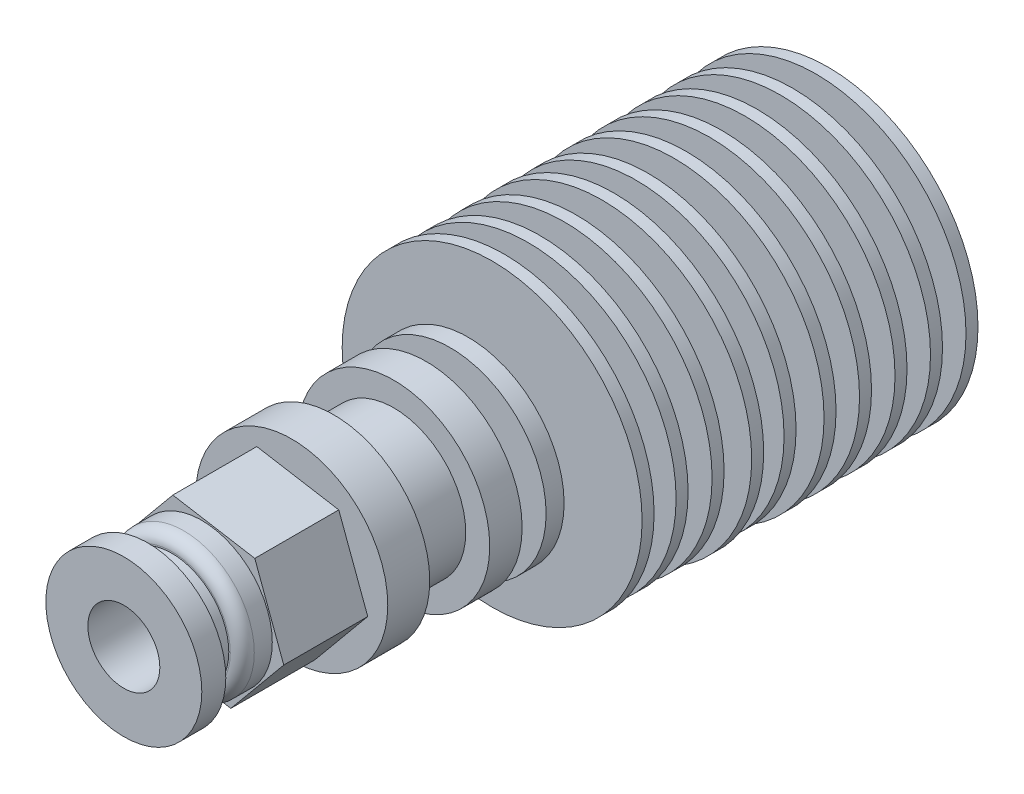
SolidWorks part; units mm, degrees
ref_plane "Front Plane" through (0, 0, 0) normal (0, 0, 1) x (1, 0, 0)
ref_plane "Top Plane" through (0, 0, 0) normal (0, 1, 0) x (1, 0, 0)
ref_plane "Right Plane" through (0, 0, 0) normal (1, 0, 0) x (0, 0, -1)
sketch "Sketch1" plane through (0, 0, 0) normal (0, 0, 1) x (1, 0, 0)
  circle A0 centre (0, 0) radius 12.5
  dimension "D1" = 25
extrude "Boss-Extrude1" add sketch "Sketch1" along normal blind 1
sketch "Sketch2" plane through (0, 0, 1) normal (0, 0, 1) x (1, 0, 0)
  circle A0 centre (0, 0) radius 7.5
  dimension "D1" = 15
extrude "Boss-Extrude2" add sketch "Sketch2" along normal blind 2
sketch "Sketch3" plane through (0, 0, 0) normal (0, 1, 0) x (1, 0, 0)
  line L0 (0, 0) -> (0.3007, -21.7542) construction
pattern_linear "LPattern2" count 5 spacing 3 along (0.0138, 0, 0.9999) of bodies 102
sketch "Sketch4" plane through (0, 0, 14.9989) normal (0, 0, 1) x (1, 0, 0)
  circle A0 centre (0, 0) radius 12.3341
extrude "Boss-Extrude3" add sketch "Sketch4" along normal blind 1
sketch "Sketch5" plane through (0, 0, 15.9989) normal (0, 0, 1) x (1, 0, 0)
  circle A0 centre (0, 0) radius 6.5
  dimension "D1" = 13
extrude "Boss-Extrude4" add sketch "Sketch5" along normal blind 2
sketch "Sketch6" plane through (0, 0, 17.9989) normal (0, 0, 1) x (1, 0, 0)
  line L0 (0, 0) -> (0.3007, 0) construction
  circle A0 centre (0.1504, 0) radius 12.4845
extrude "Boss-Extrude5" add sketch "Sketch6" along normal blind 1
sketch "Sketch7" plane through (0, 0, 18.9989) normal (0, 0, 1) x (1, 0, 0)
  circle A0 centre (0, 0) radius 5
  dimension "D1" = 10
extrude "Boss-Extrude6" add sketch "Sketch7" along normal blind 2
sketch "Sketch8" plane through (0, 0, 20.9989) normal (0, 0, 1) x (1, 0, 0)
  circle A0 centre (0, 0) radius 12.3341
extrude "Boss-Extrude7" add sketch "Sketch8" along normal blind 1
sketch "Sketch9" plane through (0, 0, 21.9989) normal (0, 0, 1) x (1, 0, 0)
  circle A0 centre (0, 0) radius 5
  dimension "D1" = 10
extrude "Boss-Extrude8" add sketch "Sketch9" along normal blind 2
sketch "Sketch10" plane through (0, 0, 23.9989) normal (0, 0, 1) x (1, 0, 0)
  circle A0 centre (0, 0) radius 12.3341
extrude "Boss-Extrude9" add sketch "Sketch10" along normal blind 1
sketch "Sketch11" plane through (0, 0, 24.9989) normal (0, 0, 1) x (1, 0, 0)
  circle A0 centre (0, 0) radius 5
  dimension "D1" = 10
extrude "Boss-Extrude10" add sketch "Sketch11" along normal blind 2
sketch "Sketch12" plane through (0, 0, 26.9989) normal (0, 0, 1) x (1, 0, 0)
  circle A0 centre (0, 0) radius 12.5
  dimension "D1" = 25
extrude "Boss-Extrude11" add sketch "Sketch12" along normal blind 1
sketch "Sketch13" plane through (0, 0, 27.9989) normal (0, 0, 1) x (1, 0, 0)
  circle A0 centre (0, 0) radius 5
  dimension "D1" = 10
extrude "Boss-Extrude12" add sketch "Sketch13" along normal blind 2
sketch "Sketch14" plane through (0, 0, 29.9989) normal (0, 0, 1) x (1, 0, 0)
  circle A0 centre (0, 0) radius 8
  dimension "D1" = 16
extrude "Boss-Extrude13" add sketch "Sketch14" along normal blind 1.5
sketch "Sketch15" plane through (0, 0, 31.4989) normal (0, 0, 1) x (1, 0, 0)
  circle A0 centre (0, 0) radius 5
  dimension "D1" = 10
extrude "Boss-Extrude14" add sketch "Sketch15" along normal blind 2
sketch "Sketch16" plane through (0, 0, 33.4989) normal (0, 0, 1) x (1, 0, 0)
  circle A0 centre (0, 0) radius 8
  dimension "D1" = 16
extrude "Boss-Extrude15" add sketch "Sketch16" along normal blind 2.7
sketch "Sketch17" plane through (0, 0, 36.1989) normal (0, 0, 1) x (1, 0, 0)
  circle A0 centre (0, 0) radius 6
  dimension "D1" = 12
extrude "Boss-Extrude16" add sketch "Sketch17" along normal blind 5
sketch "Sketch18" plane through (0, 0, 41.1989) normal (0, 0, 1) x (1, 0, 0)
  circle A0 centre (0, 0) radius 8
extrude "Boss-Extrude17" add sketch "Sketch18" along normal blind 3.5
sketch "Sketch19" plane through (0, 0, 44.6989) normal (0, 0, 1) x (1, 0, 0)
  circle A0 centre (0, 0) radius 5
  dimension "D1" = 10
extrude "Boss-Extrude18" add sketch "Sketch19" along normal blind 0.5
sketch "Sketch20" plane through (0, 0, 45.1989) normal (0, 0, 1) x (1, 0, 0)
  line L1 (2.4155, -6.4935) -> (6.8313, -1.1548)
  line L2 (6.8313, -1.1548) -> (4.4157, 5.3386)
  line L3 (4.4157, 5.3386) -> (-2.4155, 6.4935)
  line L4 (-2.4155, 6.4935) -> (-6.8313, 1.1548)
  line L5 (-6.8313, 1.1548) -> (-4.4157, -5.3386)
  line L6 (-4.4157, -5.3386) -> (2.4155, -6.4935)
  circle A0 centre (0, 0) radius 6 construction
  dimension "D1" = 12
extrude "Boss-Extrude19" add sketch "Sketch20" along normal blind 7
sketch "Sketch21" plane through (0, 0, 52.1989) normal (0, 0, 1) x (1, 0, 0)
  circle A0 centre (0, 0) radius 5.875
  dimension "D1" = 11.75
extrude "Boss-Extrude20" add sketch "Sketch21" along normal blind 2.5
sketch "Sketch22" plane through (0, 0, 54.6989) normal (0, 0, 1) x (1, 0, 0)
  circle A0 centre (0, 0) radius 4.75
  dimension "D1" = 9.5
extrude "Boss-Extrude21" add sketch "Sketch22" along normal blind 1
sketch "Sketch23" plane through (0, 0, 55.6989) normal (0, 0, 1) x (1, 0, 0)
  circle A0 centre (0, 0) radius 4
  dimension "D1" = 8
extrude "Boss-Extrude22" add sketch "Sketch23" along normal blind 1
sketch "Sketch24" plane through (0, 0, 56.6989) normal (0, 0, 1) x (1, 0, 0)
  circle A0 centre (0, 0) radius 6.5
  dimension "D1" = 13
extrude "Boss-Extrude23" add sketch "Sketch24" along normal blind 2
fillet "Fillet1" radius 1 1 edges at (5.875, 0, 54.6989)
sketch "Sketch27" plane through (0, 0, 0) normal (0, 0, -1) x (-1, 0, 0)
  circle A0 centre (0, 0) radius 2.875
  dimension "D1" = 5.75
extrude "Cut-Extrude3" cut sketch "Sketch27" against normal blind 20
sketch "Sketch28" plane through (0, 0, 20) normal (0, 0, -1) x (-1, 0, 0)
  circle A0 centre (0, 0) radius 1
  dimension "D1" = 2
extrude "Cut-Extrude4" cut sketch "Sketch28" against normal blind 35
sketch "Sketch29" plane through (0, 0, 58.6989) normal (0, 0, 1) x (1, 0, 0)
  circle A0 centre (0, 0) radius 3
  dimension "D1" = 6
extrude "Cut-Extrude5" cut sketch "Sketch29" against normal blind 35
